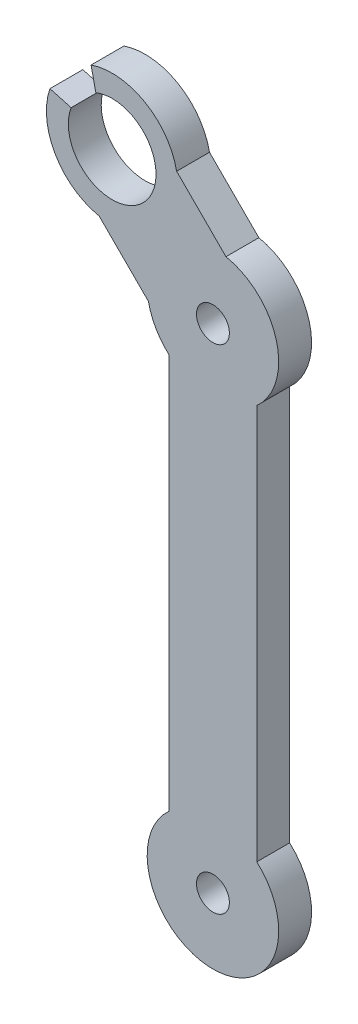
SolidWorks part; units mm, degrees
ref_plane "Plan de face" through (0, 0, 0) normal (0, 0, 1) x (1, 0, 0)
ref_plane "Plan de dessus" through (0, 0, 0) normal (0, 1, 0) x (1, 0, 0)
ref_plane "Plan de droite" through (0, 0, 0) normal (1, 0, 0) x (0, 0, -1)
sketch "Esquisse1" plane through (0, 0, 0) normal (0, 0, 1) x (1, 0, 0)
  line L0 (0, 45) -> (0, 0) construction
  line L1 (4, 40.5279) -> (4, 4.4721)
  line L2 (-4, 40.5279) -> (-4, 4.4721)
  line L3 (0, 45) -> (-9.1924, 54.1924) construction
  line L4 (-10.3827, 48.3116) -> (-5.8807, 43.8097)
  line L5 (-3.3116, 55.3827) -> (1.1903, 50.8807)
  line L6 (-13.4393, 58.4308) -> (-13.4288, 58.4413)
  line L7 (-13.4393, 58.4308) -> (-13.4279, 58.4403)
  line L8 (-10.6822, 57.9046) -> (-11.1158, 59.8757)
  line L9 (-12.939, 55.5933) -> (-14.8705, 56.1311)
  circle A0 centre (0, 0) radius 1.5
  circle A1 centre (0, 0) radius 6
  circle A2 centre (0, 45) radius 1.5
  circle A3 centre (0, 45) radius 6
  arc A4 (-14.8705, 56.1311) -> (-11.1158, 59.8757) centre (-9.1924, 54.1924) ccw
  arc A5 (-12.939, 55.5933) -> (-10.6822, 57.9046) centre (-9.1924, 54.1924) ccw
  arc A6 (-13.4288, 58.4413) -> (-13.4393, 58.4308) centre (-9.1924, 54.1924) ccw
  dimension "D1" = 3
  dimension "D3" = 12
  dimension "D4" = 3
  dimension "D5" = 45
  dimension "D2" = 12
  dimension "D6" = 4
  dimension "D7" = 4
  dimension "D8" = 135
  dimension "D9" = 13
extrude "Boss.-Extru.1" add sketch "Esquisse1" along normal blind 3 contours A3 A2 | A3 L2 A1 L1 | A1 A0 | A4 L4 A3 L5 | A5 L9 A4 L8
